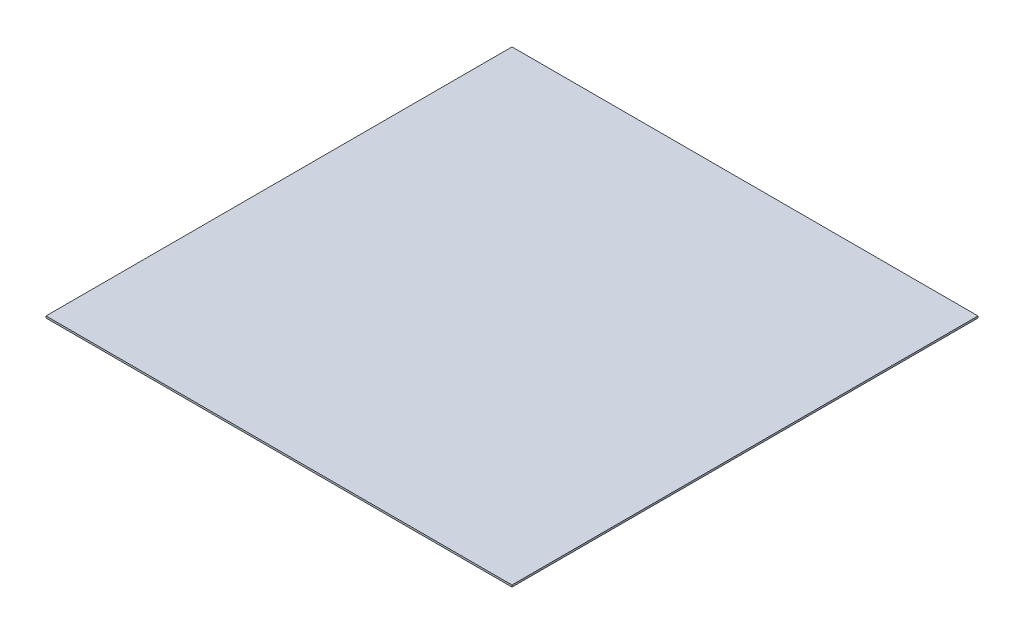
SolidWorks part; units mm, degrees
ref_plane "Płaszczyzna przednia" through (0, 0, 0) normal (0, 0, 1) x (1, 0, 0)
ref_plane "Płaszczyzna górna" through (0, 0, 0) normal (0, 1, 0) x (1, 0, 0)
ref_plane "Płaszczyzna prawa" through (0, 0, 0) normal (1, 0, 0) x (0, 0, -1)
sketch "Szkic1" plane through (0, 0, 0) normal (0, 1, 0) x (1, 0, 0)
  line L1 (-12500, -12500) -> (12500, -12500)
  line L2 (-12500, -12500) -> (-12500, 12500)
  line L3 (-12500, 12500) -> (12500, 12500)
  line L4 (12500, -12500) -> (12500, 12500)
  line L5 (-12500, -12500) -> (12500, 12500) construction
  line L6 (-12500, 12500) -> (12500, -12500) construction
  point P0 (0, 0)
  dimension "D1" = 25000
  dimension "D2" = 25000
extrude "Dodanie-wyciągnięcie1" add sketch "Szkic1" along normal blind 100
